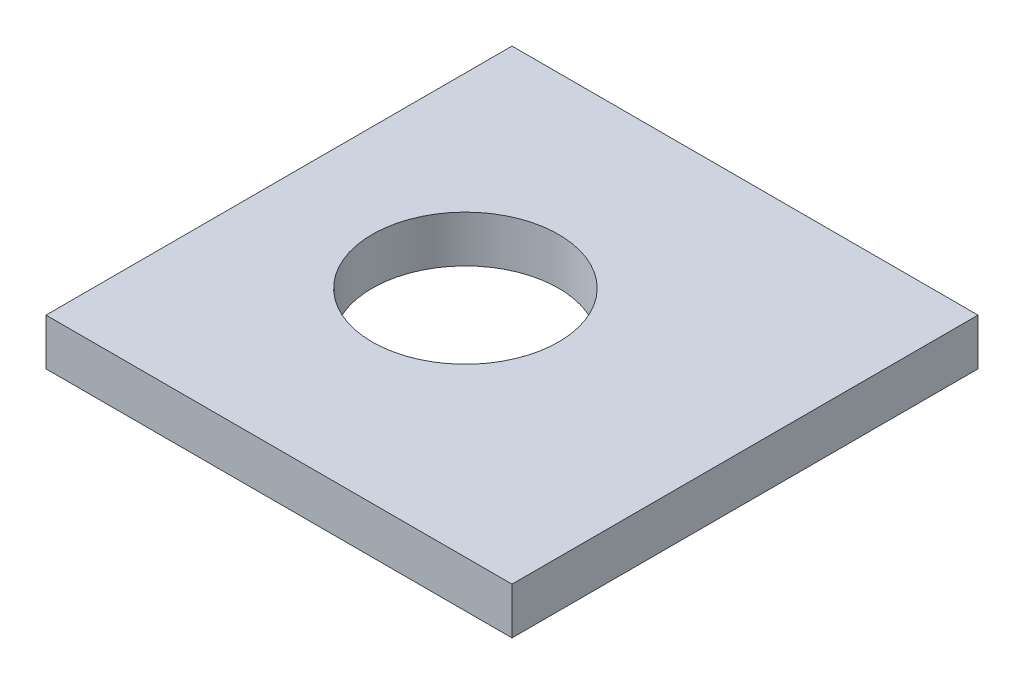
SolidWorks part; units mm, degrees
ref_plane "Спереди" through (0, 0, 0) normal (0, 0, 1) x (1, 0, 0)
ref_plane "Сверху" through (0, 0, 0) normal (0, 1, 0) x (1, 0, 0)
ref_plane "Справа" through (0, 0, 0) normal (1, 0, 0) x (0, 0, -1)
sketch "Эскиз1" plane through (0, 0, 0) normal (1, 0, 0) x (0, 0, -1)
  line L1 (15, -1.5) -> (-15, -1.5)
  line L2 (15, -1.5) -> (15, 1.5)
  line L3 (15, 1.5) -> (-15, 1.5)
  line L4 (-15, -1.5) -> (-15, 1.5)
  line L5 (15, -1.5) -> (-15, 1.5) construction
  line L6 (15, 1.5) -> (-15, -1.5) construction
  point P0 (0, 0)
extrude "Бобышка-Вытянуть1" add sketch "Эскиз1" along normal blind 30
sketch "Эскиз2" plane through (0, 1.5, 0) normal (0, 1, 0) x (1, 0, 0)
  circle A0 centre (12, 0) radius 6
extrude "Вырез-Вытянуть1" cut sketch "Эскиз2" against normal blind 30
